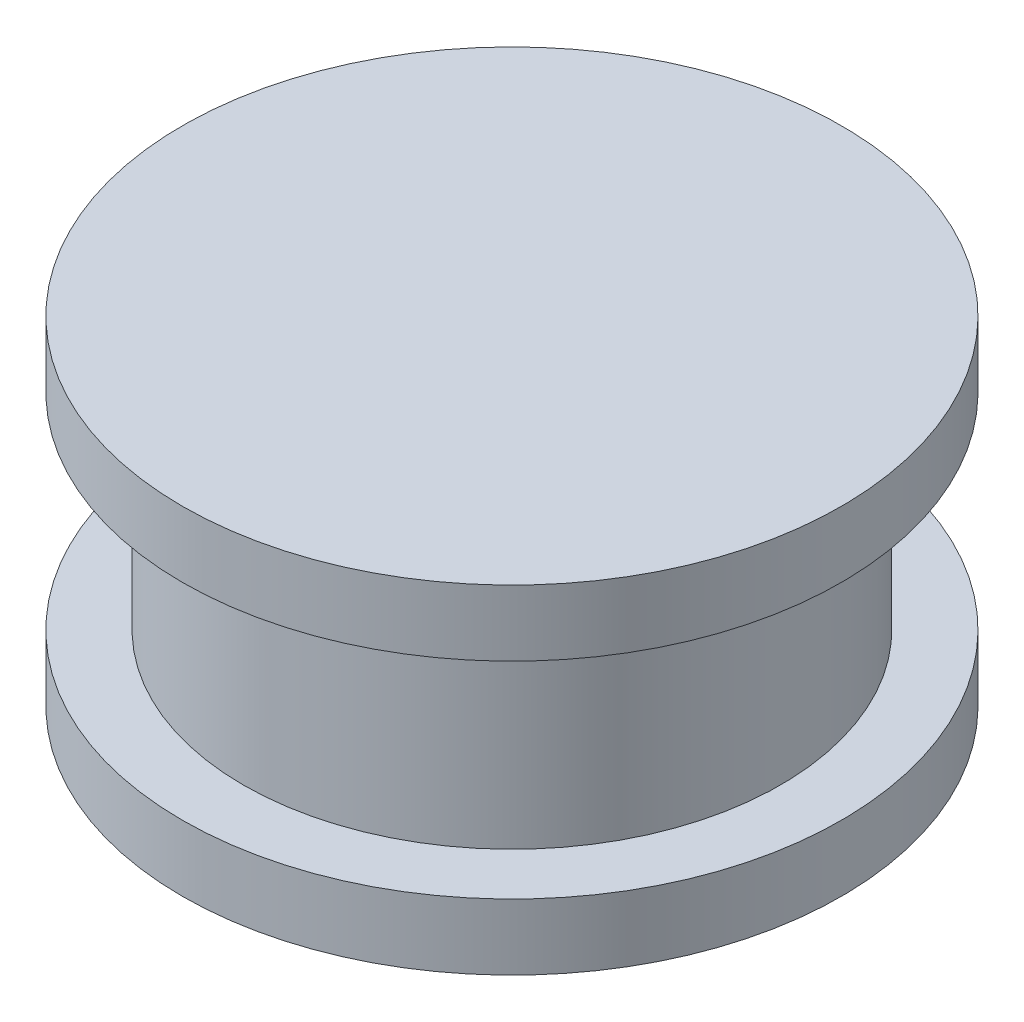
SolidWorks part; units mm, degrees
ref_plane "Front Plane" through (0, 0, 0) normal (0, 0, 1) x (1, 0, 0)
ref_plane "Top Plane" through (0, 0, 0) normal (0, 1, 0) x (1, 0, 0)
ref_plane "Right Plane" through (0, 0, 0) normal (1, 0, 0) x (0, 0, -1)
sketch "Sketch2" plane through (0, 0, 0) normal (0, 0, 1) x (1, 0, 0)
  line L0 (0, 0) -> (12.7, 0)
  line L1 (12.7, 0) -> (12.7, 2.54)
  line L2 (12.7, 2.54) -> (10.3505, 2.54)
  line L3 (10.3505, 2.54) -> (10.3505, 10.4775)
  line L4 (10.3505, 10.4775) -> (12.7, 10.4775)
  line L5 (12.7, 10.4775) -> (12.7, 13.0175)
  line L6 (12.7, 13.0175) -> (0, 13.0175)
  line L7 (0, 13.0175) -> (0, 0)
  line L8 (0, 13.0175) -> (0, 0) construction
  dimension "D1" = 10.3505
  dimension "D2" = 12.7
  dimension "D3" = 7.9375
  dimension "D4" = 2.54
  dimension "D5" = 2.54
revolve "Revolve1" add sketch "Sketch2" angle 360 about L7
